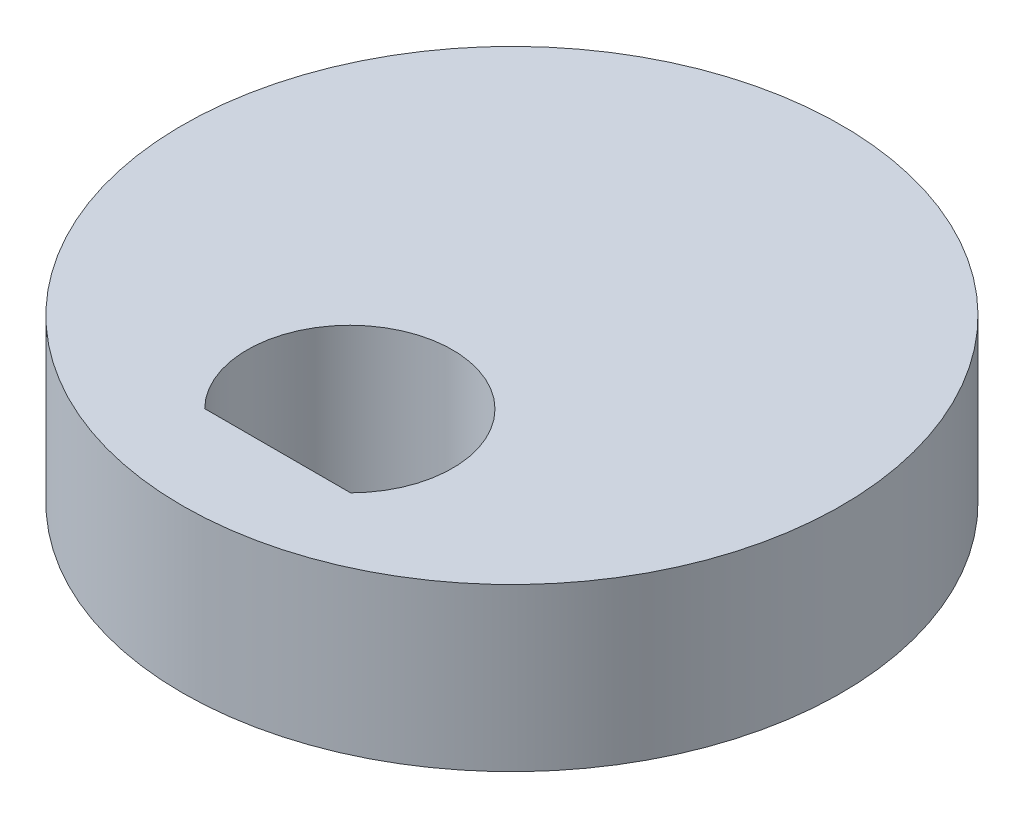
SolidWorks part; units mm, degrees
ref_plane "Front Plane" through (0, 0, 0) normal (0, 0, 1) x (1, 0, 0)
ref_plane "Top Plane" through (0, 0, 0) normal (0, 1, 0) x (1, 0, 0)
ref_plane "Right Plane" through (0, 0, 0) normal (1, 0, 0) x (0, 0, -1)
sketch "Sketch1" plane through (0, 0, 0) normal (0, 1, 0) x (1, 0, 0)
  line L0 (1.35, -4.337) -> (-1.35, -4.337)
  circle A0 centre (0, 0) radius 6.1
  arc A1 (1.35, -4.337) -> (-1.35, -4.337) centre (0, -3) ccw
  dimension "D1" = 12.2
  dimension "D3" = 2.7
  dimension "D2" = 1.9
  dimension "3" = 3
extrude "Boss-Extrude1" add sketch "Sketch1" along normal blind 3
